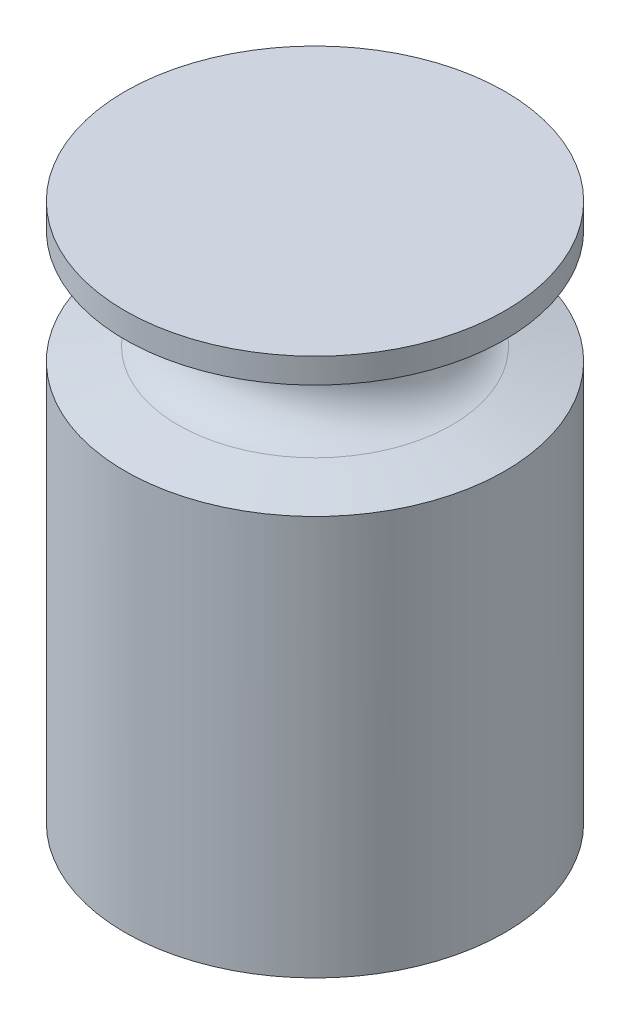
SolidWorks part; units mm, degrees
ref_plane "Front Plane" through (0, 0, 0) normal (0, 0, 1) x (1, 0, 0)
ref_plane "Top Plane" through (0, 0, 0) normal (0, 1, 0) x (1, 0, 0)
ref_plane "Right Plane" through (0, 0, 0) normal (1, 0, 0) x (0, 0, -1)
sketch "Sketch1" plane through (0, 0, 0) normal (0, 1, 0) x (1, 0, 0)
  circle A0 centre (0, 0) radius 25.05
extrude "Boss-Extrude1" add sketch "Sketch1" along normal blind 71
sketch "Sketch2" plane through (0, 0, 0) normal (0, 0, 1) x (1, 0, 0)
  line L0 (-25.05, 67.7) -> (-18.0451, 65.9535)
  line L1 (-25.05, 71) -> (-25.05, 0) construction
  line L2 (-25.05, 52.7) -> (-18.0451, 54.4465)
  line L3 (-25.05, 67.7) -> (-25.05, 52.7)
  line L6 (0, -27.555) -> (0, 27.555) construction
  arc A0 (-18.0451, 65.9535) -> (-18.0451, 54.4465) centre (-19.4796, 60.2) cw
  point P7 (-13.55, 60.2)
  dimension "D1" = 3.3
  dimension "D2" = 18.3
  dimension "D3" = 13.55
ref_axis "Axis1" through (0, -3.55, 0) along (0, 1, 0)
revolve "Cut-Revolve1" cut sketch "Sketch2" angle 360 about axis through (0, -3.55, 0) along (0, 1, 0)
